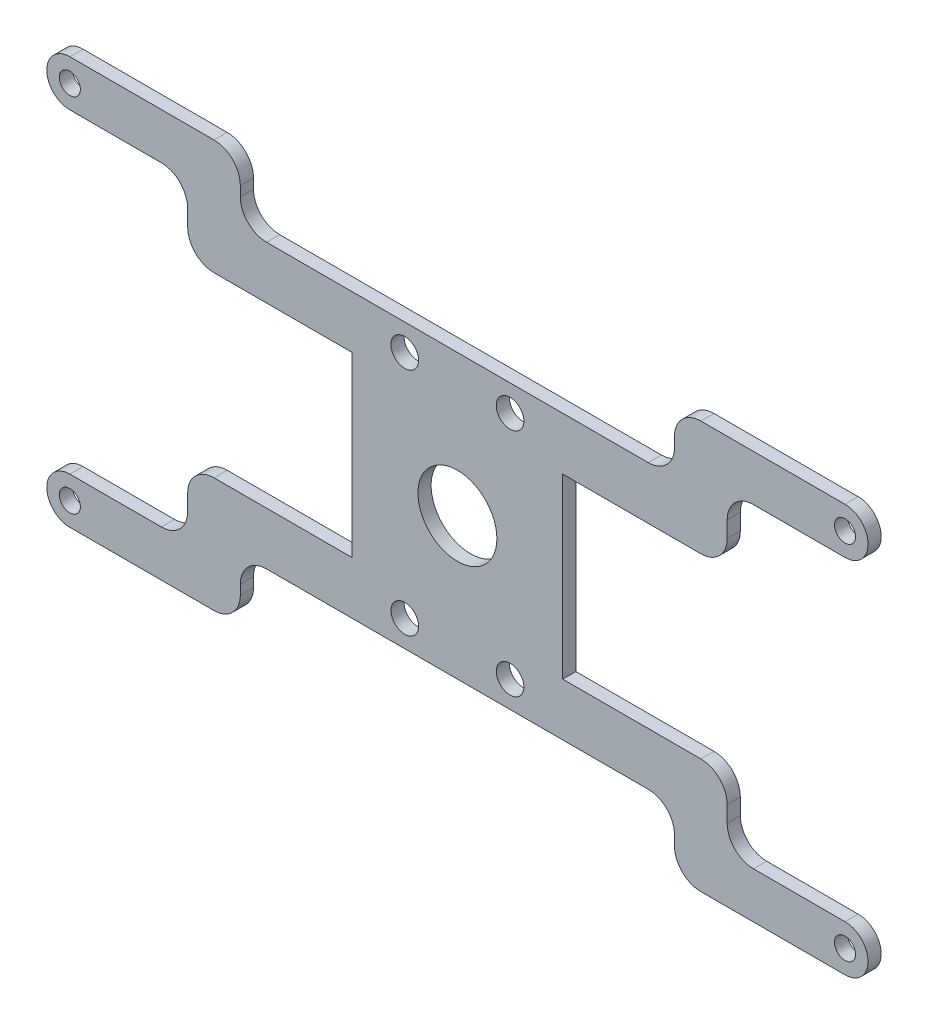
SolidWorks part; units mm, degrees
ref_plane "Front Plane" through (0, 0, 0) normal (0, 0, 1) x (1, 0, 0)
ref_plane "Top Plane" through (0, 0, 0) normal (0, 1, 0) x (1, 0, 0)
ref_plane "Right Plane" through (0, 0, 0) normal (1, 0, 0) x (0, 0, -1)
sketch "Sketch1" plane through (0, 0, 0) normal (0, 0, 1) x (1, 0, 0)
  line L1 (0, 0) -> (0, 3.5)
  line L4 (0, 0) -> (0, 54.9422)
  line L5 (0, 3.5) -> (37.9119, 3.5)
  line L6 (79.9119, 40.9711) -> (79.9119, 13.9711)
  line L7 (0, 51.4422) -> (37.9119, 51.4422)
  line L9 (45.9119, 51.4422) -> (45.9119, 58.4422)
  line L10 (117.8238, 58.4422) -> (71.9119, 58.4422)
  line L11 (66.9119, 5.9711) -> (71.9119, 5.9711)
  line L12 (71.9119, 5.9711) -> (71.9119, 3.5)
  line L13 (117.8238, -3.5) -> (71.9119, -3.5)
  line L15 (66.9119, 40.9711) -> (50.9119, 40.9711)
  line L17 (66.9119, 48.9711) -> (50.9119, 48.9711)
  line L18 (66.9119, 13.9711) -> (50.9119, 13.9711)
  line L19 (66.9119, 5.9711) -> (50.9119, 5.9711)
  line L22 (71.9119, 27.4711) -> (71.9119, 40.9711)
  line L23 (66.9119, 13.9711) -> (71.9119, 13.9711)
  line L24 (79.9119, 13.9711) -> (79.9119, 3.5)
  line L25 (71.9119, 3.5) -> (71.9119, -3.5)
  line L26 (79.9119, 3.5) -> (117.8238, 3.5)
  line L27 (71.9119, 27.4711) -> (71.9119, 13.9711)
  line L28 (50.9119, 5.9711) -> (45.9119, 5.9711)
  line L29 (45.9119, 5.9711) -> (45.9119, 3.5)
  line L30 (50.9119, 13.9711) -> (45.9119, 13.9711)
  line L31 (37.9119, 13.9711) -> (37.9119, 3.5)
  line L32 (79.9119, 40.9711) -> (79.9119, 51.4422)
  line L33 (66.9119, 40.9711) -> (71.9119, 40.9711)
  line L34 (66.9119, 48.9711) -> (71.9119, 48.9711)
  line L35 (71.9119, 48.9711) -> (71.9119, 51.4422)
  line L36 (50.9119, 48.9711) -> (45.9119, 48.9711)
  line L37 (45.9119, 48.9711) -> (45.9119, 51.4422)
  line L38 (37.9119, 40.9711) -> (37.9119, 51.4422)
  line L39 (50.9119, 40.9711) -> (45.9119, 40.9711)
  line L41 (45.9119, 3.5) -> (45.9119, -3.5)
  line L42 (45.9119, -3.5) -> (0, -3.5)
  line L43 (71.9119, 51.4422) -> (71.9119, 58.4422)
  line L44 (45.9119, 58.4422) -> (0, 58.4422)
  line L45 (79.9119, 51.4422) -> (117.8238, 51.4422)
  line L46 (37.9119, 40.9711) -> (37.9119, 13.9711)
  line L48 (45.9119, 27.4711) -> (45.9119, 40.9711)
  line L49 (45.9119, 27.4711) -> (45.9119, 13.9711)
  circle A0 centre (0, 54.9422) radius 1.6
  circle A1 centre (117.8238, 54.9422) radius 1.6
  circle A2 centre (117.8238, 0) radius 1.6
  circle A3 centre (0, 0) radius 1.6
  arc A4 (0, 58.4422) -> (0, 51.4422) centre (0, 54.9422) ccw
  arc A5 (117.8238, 51.4422) -> (117.8238, 58.4422) centre (117.8238, 54.9422) ccw
  arc A6 (117.8238, -3.5) -> (117.8238, 3.5) centre (117.8238, 0) ccw
  arc A7 (0, 3.5) -> (0, -3.5) centre (0, 0) ccw
  circle A8 centre (66.9119, 44.9711) radius 2.1
  circle A9 centre (66.9119, 9.9711) radius 2.1
  circle A14 centre (50.9119, 9.9711) radius 2.1
  circle A15 centre (50.9119, 44.9711) radius 2.1
  point P32 (58.9119, 40.9711)
  point P34 (58.9119, 48.9711)
  point P36 (58.9119, 13.9711)
  point P41 (58.9119, 5.9711)
  dimension "D1" = 54.9422
  dimension "D2" = 3.5
  dimension "D3" = 117.8238
extrude "Boss-Extrude3" add sketch "Sketch1" along normal blind 2
sketch "Sketch3" plane through (0, 0, 2) normal (0, 0, 1) x (1, 0, 0)
  line L0 (71.9119, 13.9711) -> (99.9119, 13.9711)
  line L1 (99.9119, 13.9711) -> (99.9119, 3.5)
  line L2 (79.9119, 3.5) -> (117.8238, 3.5) construction
  line L3 (71.9119, 13.9711) -> (71.9119, 5.9711)
  line L4 (71.9119, 5.9711) -> (91.9119, 5.9711)
  line L5 (91.9119, 5.9711) -> (91.9119, 3.5)
  line L6 (91.9119, 3.5) -> (99.9119, 3.5)
  line L12 (91.9119, 51.4422) -> (99.9119, 51.4422)
  line L13 (91.9119, 48.9711) -> (91.9119, 51.4422)
  line L14 (71.9119, 48.9711) -> (91.9119, 48.9711)
  line L15 (71.9119, 40.9711) -> (71.9119, 48.9711)
  line L16 (99.9119, 40.9711) -> (99.9119, 51.4422)
  line L17 (71.9119, 40.9711) -> (99.9119, 40.9711)
  line L18 (45.9119, 40.9711) -> (17.9119, 40.9711)
  line L19 (17.9119, 40.9711) -> (17.9119, 51.4422)
  line L20 (45.9119, 40.9711) -> (45.9119, 48.9711)
  line L21 (45.9119, 48.9711) -> (25.9119, 48.9711)
  line L22 (25.9119, 48.9711) -> (25.9119, 51.4422)
  line L23 (25.9119, 51.4422) -> (17.9119, 51.4422)
  line L24 (25.9119, 3.5) -> (17.9119, 3.5)
  line L25 (25.9119, 5.9711) -> (25.9119, 3.5)
  line L26 (45.9119, 5.9711) -> (25.9119, 5.9711)
  line L27 (45.9119, 13.9711) -> (45.9119, 5.9711)
  line L28 (17.9119, 13.9711) -> (17.9119, 3.5)
  line L29 (45.9119, 13.9711) -> (17.9119, 13.9711)
extrude "Boss-Extrude4" add sketch "Sketch3" against normal up to surface (2 mm away) up to face at (58.9119, 27.4711, 0)
sketch "Sketch4" plane through (0, 0, 2) normal (0, 0, 1) x (1, 0, 0)
  line L0 (25.9119, 48.9711) -> (25.9119, 65.3112)
  line L1 (25.9119, 48.9711) -> (91.9119, 48.9711)
  line L2 (91.9119, 48.9711) -> (91.9119, 65.3112)
  line L3 (91.9119, 65.3112) -> (25.9119, 65.3112)
  line L4 (25.9119, 5.9711) -> (91.9119, 5.9711)
  line L5 (91.9119, 5.9711) -> (91.9119, -18.7705)
  line L6 (91.9119, -18.7705) -> (25.9119, -18.7705)
  line L7 (25.9119, -18.7705) -> (25.9119, 5.9711)
extrude "Cut-Extrude3" cut sketch "Sketch4" against normal blind 14.5
fillet "Fillet1" radius 4 16 edges at (25.9119, 48.9711, 1) (25.9119, 58.4422, 1) (17.9119, 51.4422, 1) (17.9119, 40.9711, 1) (25.9119, 5.9711, 1) (25.9119, -3.5, 1) (17.9119, 3.5, 1) (17.9119, 13.9711, 1) (99.9119, 13.9711, 1) (99.9119, 3.5, 1) (91.9119, 5.9711, 1) (91.9119, -3.5, 1) (99.9119, 40.9711, 1) (99.9119, 51.4422, 1) (91.9119, 48.9711, 1) (91.9119, 58.4422, 1)
sketch "Sketch5" plane through (0, 0, 2) normal (0, 0, 1) x (1, 0, 0)
  line L0 (45.9119, 40.9711) -> (45.9119, 13.9711)
  line L3 (45.9119, 13.9711) -> (71.9119, 13.9711)
  line L5 (71.9119, 13.9711) -> (71.9119, 40.9711)
  line L6 (71.9119, 40.9711) -> (45.9119, 40.9711)
  circle A0 centre (58.9119, 27.4711) radius 6
extrude "Boss-Extrude5" add sketch "Sketch5" against normal up to surface (2 mm away) up to face at (58.9119, 27.4711, 0)
sketch "Sketch6" plane through (0, 0, 2) normal (0, 0, 1) x (1, 0, 0)
  line L0 (37.9119, 40.9711) -> (42.9119, 40.9711)
  line L1 (37.9119, 13.9711) -> (42.9119, 13.9711)
  line L2 (42.9119, 13.9711) -> (42.9119, 40.9711)
  line L3 (37.9119, 40.9711) -> (37.9119, 13.9711)
  line L4 (79.9119, 13.9711) -> (74.9119, 13.9711)
  line L5 (74.9119, 13.9711) -> (74.9119, 40.9711)
  line L6 (74.9119, 40.9711) -> (79.9119, 40.9711)
  line L7 (79.9119, 40.9711) -> (79.9119, 13.9711)
extrude "Cut-Extrude4" cut sketch "Sketch6" against normal blind 14.5
